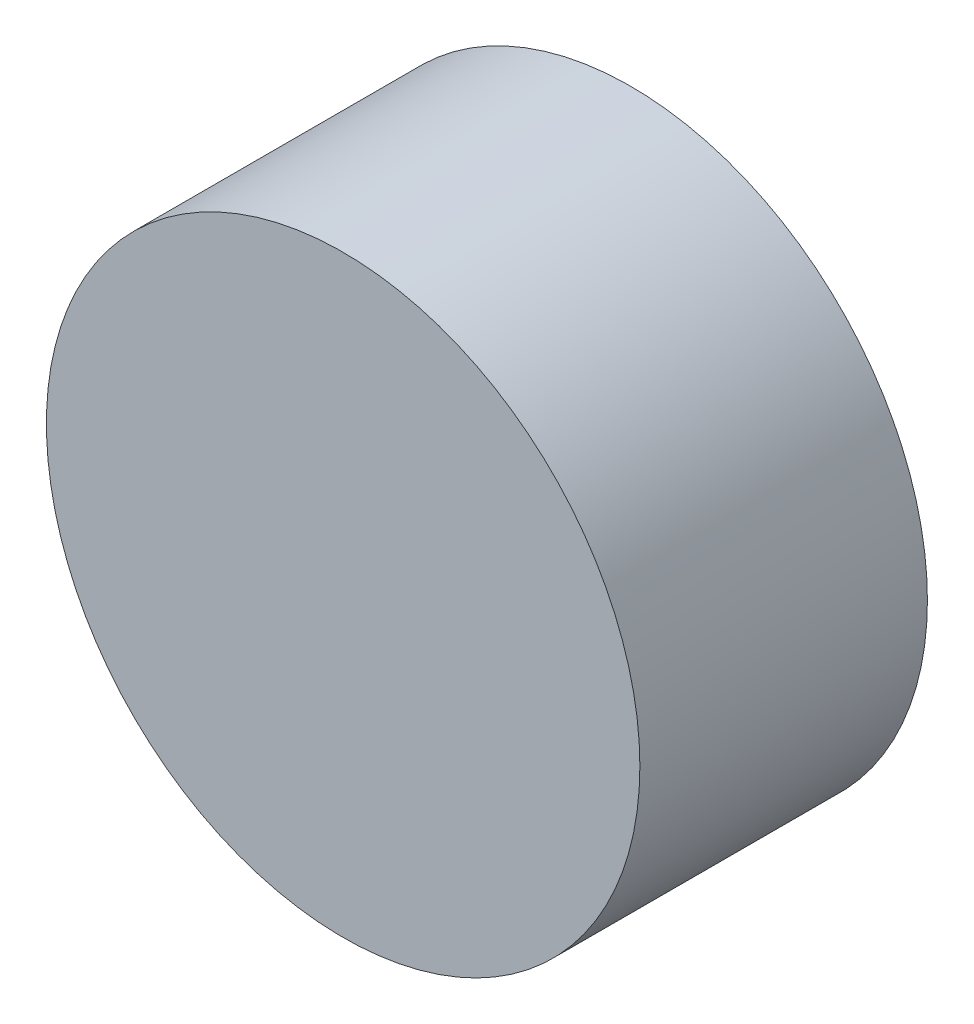
SolidWorks part; units mm, degrees
ref_plane "Front" through (0, 0, 0) normal (0, 0, 1) x (1, 0, 0)
ref_plane "Top" through (0, 0, 0) normal (0, 1, 0) x (1, 0, 0)
ref_plane "Right" through (0, 0, 0) normal (1, 0, 0) x (0, 0, -1)
sketch "Sketch1" plane through (0, 0, 0) normal (0, 0, 1) x (1, 0, 0)
  circle A1 centre (0, 0) radius 3.2766
extrude "Boss-Extrude1" add sketch "Sketch1" along normal blind 3.175
